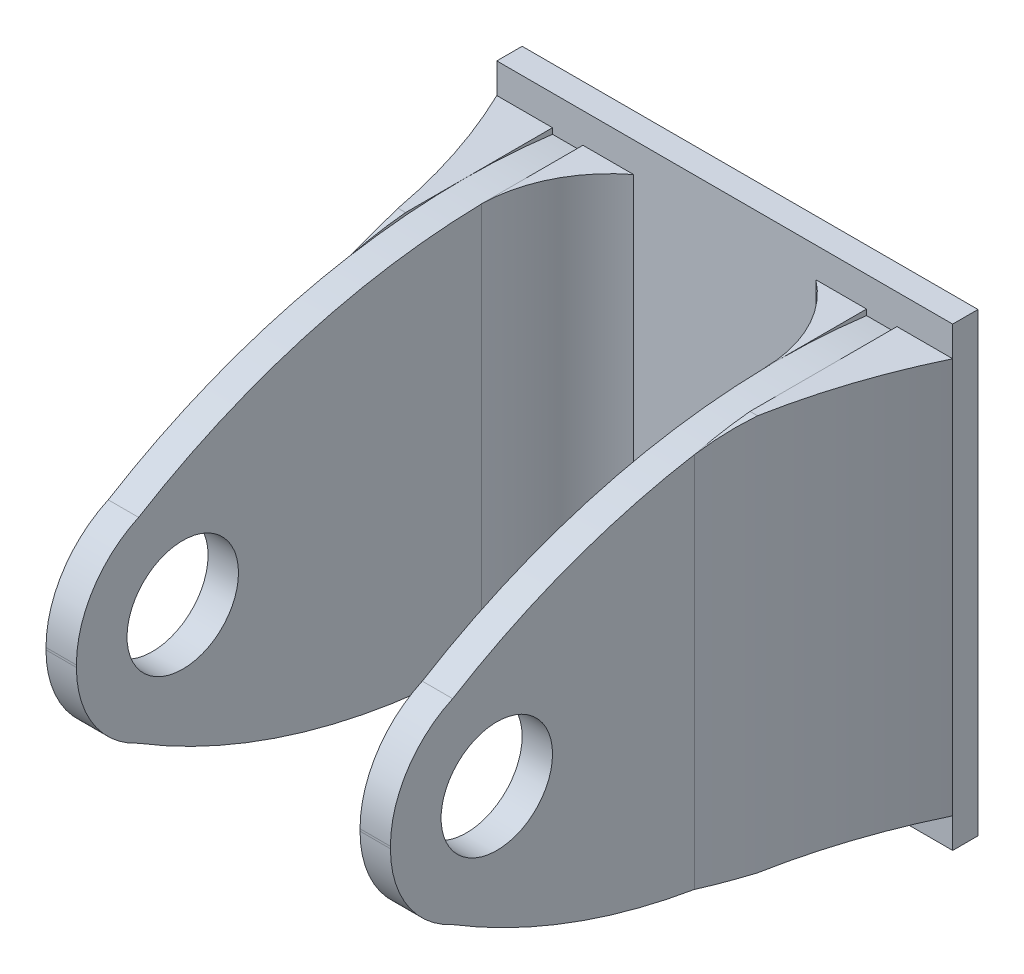
SolidWorks part; units mm, degrees
ref_plane "前视基准面" through (0, 0, 0) normal (0, 0, 1) x (1, 0, 0)
ref_plane "上视基准面" through (0, 0, 0) normal (0, 1, 0) x (1, 0, 0)
ref_plane "右视基准面" through (0, 0, 0) normal (1, 0, 0) x (0, 0, -1)
sketch "草图1" plane through (0, 0, 0) normal (0, 0, 1) x (1, 0, 0)
  line L1 (0, 0) -> (45, 0)
  line L2 (0, 0) -> (0, 45)
  line L3 (0, 45) -> (45, 45)
  line L4 (45, 0) -> (45, 45)
  dimension "D1" = 45
extrude "凸台-拉伸1" add sketch "草图1" along normal blind 2.5
ref_plane "基准面1" through (0, 0, 2.5) normal (0, 0, 1) x (1, 0, 0)
sketch "草图2" plane through (0, 0, 2.5) normal (0, 0, 1) x (1, 0, 0)
  line L0 (22.5, 45) -> (22.5, 12.6233) construction
  line L1 (45, 45) -> (0, 45) construction
  line L2 (0, 22.5) -> (22.5, 22.5) construction
  line L3 (0, 45) -> (0, 0) construction
  line L4 (22.5, 22.5) -> (36.5, 22.5) construction
  line L5 (36.5, 22.5) -> (36.5, 0)
  line L6 (0, 0) -> (45, 0) construction
  line L7 (36.5, 0) -> (39.5, 0)
  line L8 (39.5, 0) -> (39.5, 45)
  line L9 (39.5, 45) -> (36.5, 45)
  line L10 (36.5, 45) -> (36.5, 22.5)
  line L11 (8.5, 45) -> (8.5, 22.5)
  line L12 (5.5, 45) -> (8.5, 45)
  line L13 (5.5, 0) -> (5.5, 45)
  line L14 (8.5, 0) -> (5.5, 0)
  line L15 (8.5, 22.5) -> (8.5, 0)
  dimension "D1" = 14
  dimension "D2" = 3
extrude "凸台-拉伸2" add sketch "草图2" along normal blind 50
ref_plane "基准面2" through (39.5, 0, 0) normal (1, 0, 0) x (0, 0, -1)
sketch "草图3" plane through (39.5, 0, 0) normal (1, 0, 0) x (0, 0, -1)
  line L0 (-52.5, 22.5) -> (-42, 22.5) construction
  line L1 (-52.5, 0) -> (-52.5, 45) construction
  line L2 (-27.5, 45) -> (-27.5, 22.5) construction
  line L3 (-52.5, 45) -> (-2.5, 45) construction
  circle A0 centre (-42, 22.5) radius 5.5
  circle A1 centre (-42, 22.5) radius 10.5 construction
  dimension "D2" = 11
  dimension "D3" = 21
  dimension "D1" = 10.5
extrude "切除-拉伸1" cut sketch "草图3" against normal through all
sketch "草图4" plane through (39.5, 0, 0) normal (1, 0, 0) x (0, 0, -1)
  line L0 (-2.5, 45) -> (-2.5, 41.4742)
  line L1 (-42, 22.605) -> (-52.5, 22.605) construction
  line L2 (-2.5, 27.2281) -> (-2.5, -27.2281) construction
  line L3 (-52.5, 22.605) -> (-52.5, 45)
  line L4 (-52.5, 45) -> (-2.5, 45)
  line L5 (-2.5, 22.5) -> (-57.8273, 22.5) construction
  line L7 (-52.5, 0) -> (-52.5, 45) construction
  line L8 (-52.5, 22.395) -> (-52.5, 0)
  line L9 (-52.5, 0) -> (-2.5, 0)
  line L10 (-2.5, 0) -> (-2.5, 3.5258)
  arc A0 (-46.3587, 32.1576) -> (-52.5, 22.605) centre (-42, 22.605) ccw
  arc A1 (-46.3587, 32.1576) -> (-2.5, 41.4742) centre (-11.2034, -25.4458) cw
  arc A2 (-46.3587, 12.8424) -> (-52.5, 22.395) centre (-42, 22.395) cw
  arc A3 (-46.3587, 12.8424) -> (-2.5, 3.5258) centre (-11.2034, 70.4458) ccw
  dimension "D1" = 10.5
extrude "切除-拉伸2" cut sketch "草图4" against normal through all
ref_plane "基准面3" through (0, 0, 2.5) normal (0, 0, 1) x (1, 0, 0)
sketch "草图5" plane through (0, 0, 2.5) normal (0, 0, 1) x (1, 0, 0)
  line L0 (7, 2.9622) -> (13.5, 2.9622) construction
  line L1 (5.5, 2.9622) -> (8.5, 2.9622) construction
  line L2 (22.5, 45) -> (22.5, 26.1335) construction
  line L3 (8.5, 42.0378) -> (13.5, 42.0378)
  line L4 (8.5, 42.0378) -> (8.5, 2.9622)
  line L5 (8.5, 2.9622) -> (13.5, 2.9622)
  line L6 (13.5, 42.0378) -> (13.5, 2.9622)
  line L7 (45, 45) -> (0, 45) construction
  line L8 (36.5, 2.9622) -> (31.5, 2.9622)
  line L9 (31.5, 42.0378) -> (31.5, 2.9622)
  line L10 (36.5, 42.0378) -> (31.5, 42.0378)
  line L11 (36.5, 42.0378) -> (36.5, 2.9622)
  dimension "D1" = 5
extrude "凸台-拉伸3" add sketch "草图5" along normal blind 10
ref_plane "基准面4" through (0, 42.0378, 0) normal (0, 1, 0) x (1, 0, 0)
sketch "草图6" plane through (0, 42.0378, 0) normal (0, 1, 0) x (1, 0, 0)
  line L0 (-27.2281, -2.5) -> (27.2281, -2.5) construction
  line L1 (22.5, 0) -> (22.5, -12.7067) construction
  line L2 (13.5, -2.5) -> (13.5, -12.5)
  line L3 (13.5, -12.5) -> (8.5, -12.5)
  line L4 (45, 0) -> (0, 0) construction
  line L5 (31.5, -2.5) -> (31.5, -12.5)
  line L6 (31.5, -12.5) -> (36.5, -12.5)
  arc A0 (8.5, -12.5) -> (13.5, -2.5) centre (21.4135, -12.7067) cw
  arc A1 (36.5, -12.5) -> (31.5, -2.5) centre (23.5865, -12.7067) ccw
extrude "切除-拉伸3" cut sketch "草图6" against normal through all
sketch "草图7" plane through (0, 0, 2.5) normal (0, 0, 1) x (1, 0, 0)
  line L0 (5.5, 2.9622) -> (0, 2.9622)
  line L1 (0, 45) -> (0, 0) construction
  line L2 (0, 2.9622) -> (0, 42.0378)
  line L3 (7.5018, 42.0378) -> (-7.5018, 42.0378) construction
  line L4 (0, 42.0378) -> (5.5, 42.0378)
  line L5 (5.5, 42.0378) -> (5.5, 32.1576) construction
  line L6 (5.5, 42.0378) -> (5.5, 2.9622)
  line L7 (45, 45) -> (0, 45) construction
  line L8 (22.5, 45) -> (22.5, 17.548) construction
  line L9 (45, 42.0378) -> (39.5, 42.0378)
  line L10 (45, 2.9622) -> (45, 42.0378)
  line L11 (39.5, 2.9622) -> (45, 2.9622)
  line L12 (39.5, 42.0378) -> (39.5, 2.9622)
extrude "凸台-拉伸4" add sketch "草图7" along normal blind 20
ref_plane "基准面5" through (45, 0, 0) normal (1, 0, 0) x (0, 0, -1)
sketch "草图8" plane through (45, 0, 0) normal (1, 0, 0) x (0, 0, -1)
  line L0 (7.5018, 42.0378) -> (-7.5018, 42.0378) construction
  line L1 (-22.5, 41.0856) -> (-22.5, 42.0378)
  line L2 (-22.5, 42.0378) -> (-17.0082, 42.0378)
  line L3 (-22.5, 22.5) -> (-17.0082, 22.5) construction
  line L4 (-22.5, 41.0856) -> (-22.5, 3.9144) construction
  line L5 (-22.5, 3.9144) -> (-22.5, 2.9622)
  line L6 (-22.5, 2.9622) -> (-17.0082, 2.9622)
  arc A0 (-22.5, 41.0856) -> (-17.0082, 42.0378) centre (-13.2942, 4.3055) cw
  arc A1 (-22.5, 3.9144) -> (-17.0082, 2.9622) centre (-13.2942, 40.6945) ccw
extrude "切除-拉伸4" cut sketch "草图8" against normal through all
ref_plane "基准面6" through (0, 2.9622, 0) normal (0, -1, 0) x (-1, 0, 0)
sketch "草图9" plane through (0, 2.9622, 0) normal (0, -1, 0) x (-1, 0, 0)
  line L0 (-39.5, 31.1415) -> (-39.5, -31.1415) construction
  line L1 (-45, -22.5) -> (-39.5, -22.5) construction
  line L2 (-45, 1.375) -> (-45, -1.375) construction
  line L3 (-32.441, -2.5) -> (32.441, -2.5) construction
  line L6 (0, 0) -> (-45, 0) construction
  line L7 (-22.5, 0) -> (-22.5, -19.4482) construction
  line L8 (-39.5, -22.5) -> (-45, -22.5)
  line L9 (-45, -22.5) -> (-45, -2.5)
  line L10 (-5.5, -22.5) -> (0, -22.5)
  line L11 (0, -22.5) -> (0, -2.5)
  arc A0 (-39.5, -22.5) -> (-45, -2.5) centre (-96.727, -27.4812) ccw
  arc A1 (-5.5, -22.5) -> (0, -2.5) centre (51.727, -27.4812) cw
extrude "切除-拉伸5" cut sketch "草图9" against normal through all
